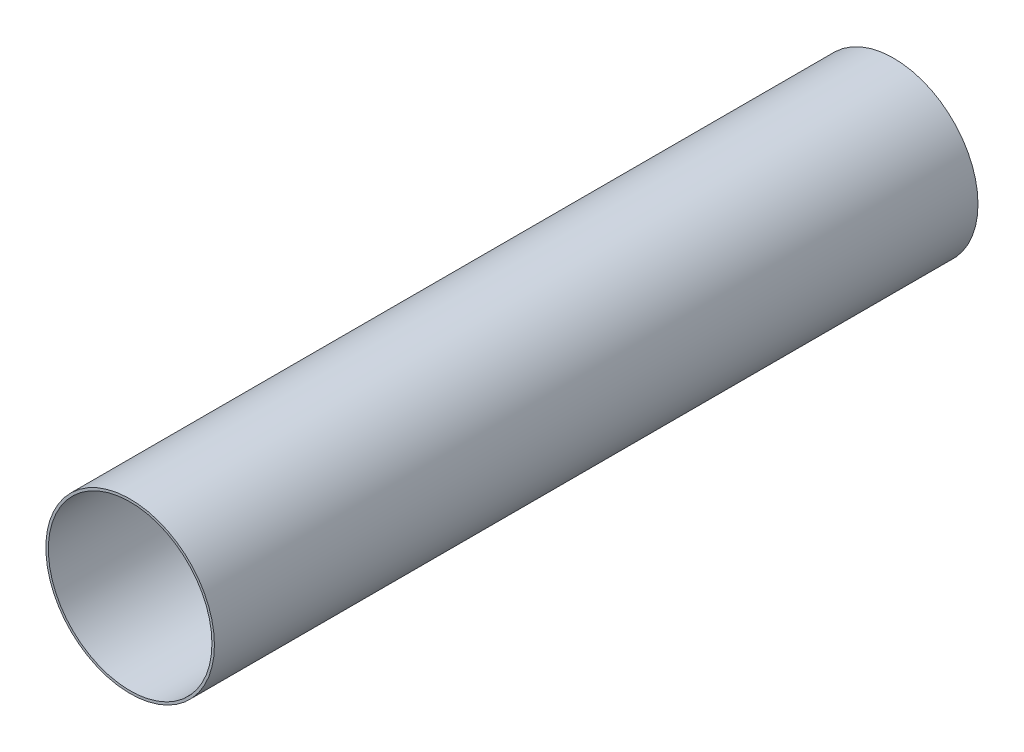
SolidWorks part; units mm, degrees
ref_plane "Front Plane" through (0, 0, 0) normal (0, 0, 1) x (1, 0, 0)
ref_plane "Top Plane" through (0, 0, 0) normal (0, 1, 0) x (1, 0, 0)
ref_plane "Right Plane" through (0, 0, 0) normal (1, 0, 0) x (0, 0, -1)
sketch "Sketch1" plane through (0, 0, 0) normal (0, 0, 1) x (1, 0, 0)
  circle A0 centre (0, 0) radius 39.2557
  circle A1 centre (0, 0) radius 38.1
  dimension "D1" = 76.2
  dimension "D2" = 78.5114
extrude "Boss-Extrude1" add sketch "Sketch1" along normal mid plane 355.6
equation "\"AIRFRAME_OD\"= 3.091in"
equation "\"AIRFRAME_ID\"= 3.00in"
equation "\"FLAT_T\"= 0.125in"
equation "\"NOSE_EXP_L\"= 3.5in"
equation "\"NOSE_SHOULDER_L\"= 5in"
equation "\"MAIN_L\"= 30in"
equation "\"RECO_COUP_L\"= 6in"
equation "\"RECO_SWITCH_L\"= 1.5in"
equation "\"DROGUE_L\"= 14in"
equation "\"ATS_FORE_COUP_L\"= 4in"
equation "\"ATS_AFT_COUP_L\"= 2.5in"
equation "\"LOWER_L\"= 16in"
equation "\"FIN_N\"= 4"
equation "\"CR_AFT_X\"= 0.5in"
equation "\"CR_FORE_X\"= 6in"
equation "\"D1@Sketch1\"=\"AIRFRAME_ID\""
equation "\"D2@Sketch1\"=\"AIRFRAME_OD\""
equation "\"D1@Boss-Extrude1\"=\"DROGUE_L\""
equation "\"FIN_ROOT\"= 5in"
equation "\"FIN_X\"= 0.75in"
equation "\"MOTOR_OD\"= 2.25in"
equation "\"MOTOR_ID\"= 2.126in"
